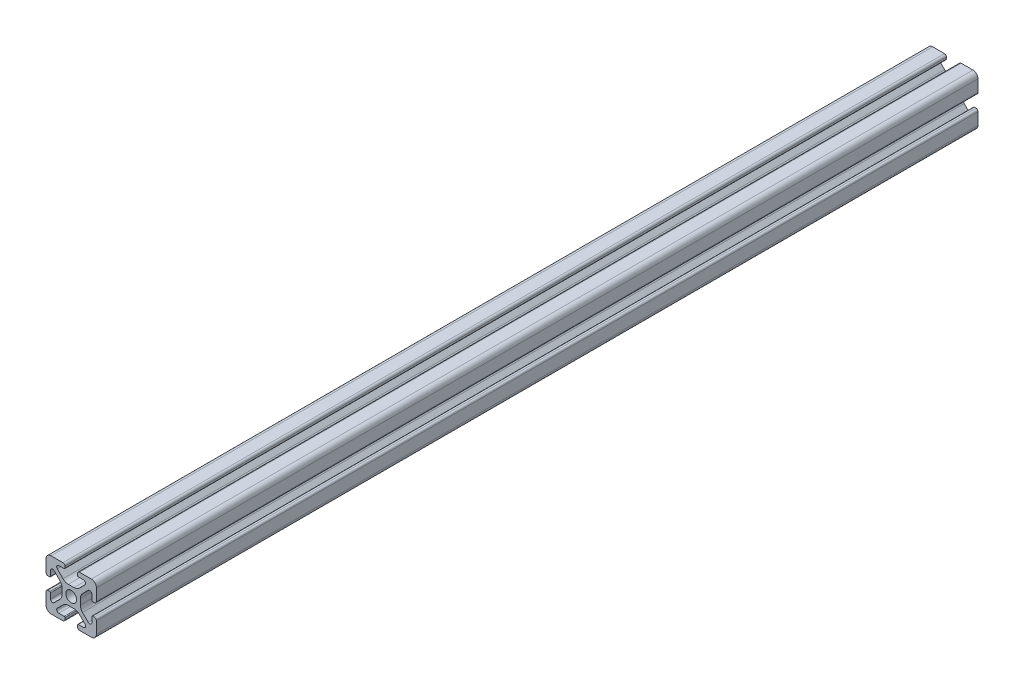
SolidWorks part; units mm, degrees
ref_plane "Front Plane" through (0, 0, 0) normal (0, 0, 1) x (1, 0, 0)
ref_plane "Top Plane" through (0, 0, 0) normal (0, 1, 0) x (1, 0, 0)
ref_plane "Right Plane" through (0, 0, 0) normal (1, 0, 0) x (0, 0, -1)
sketch "Sketch1" plane through (0, 0, 0) normal (0, 0, 1) x (1, 0, 0)
  line L2 (-9.9949, 7.9883) -> (-9.9949, 3.2893)
  line L3 (-7.9883, 9.9949) -> (-3.2893, 9.9949)
  line L4 (-2.5019, 9.2075) -> (-2.5019, 8.4963)
  line L5 (-2.8067, 8.1915) -> (-4.9149, 8.1915)
  line L6 (-5.5076, 6.7606) -> (-3.2528, 4.5058)
  line L7 (-6.7606, 5.5076) -> (-4.5058, 3.2528)
  line L8 (-8.1915, 4.9149) -> (-8.1915, 2.8067)
  line L9 (-8.4963, 2.5019) -> (-9.2075, 2.5019)
  line L11 (-1.1334, 3.6279) -> (1.1334, 3.6279)
  line L12 (-3.6279, 1.1334) -> (-3.6279, -1.1334)
  line L13 (8.4963, 2.5019) -> (9.2075, 2.5019)
  line L14 (8.1915, 4.9149) -> (8.1915, 2.8067)
  line L15 (9.9949, 7.9883) -> (9.9949, 3.2893)
  line L16 (7.9883, 9.9949) -> (3.2893, 9.9949)
  line L17 (2.5019, 9.2075) -> (2.5019, 8.4963)
  line L18 (2.8067, 8.1915) -> (4.9149, 8.1915)
  line L19 (3.6279, 1.1334) -> (3.6279, -1.1334)
  line L20 (5.5076, 6.7606) -> (3.2528, 4.5058)
  line L21 (6.7606, 5.5076) -> (4.5058, 3.2528)
  line L22 (-8.4963, -2.5019) -> (-9.2075, -2.5019)
  line L23 (-8.1915, -4.9149) -> (-8.1915, -2.8067)
  line L24 (-6.7606, -5.5076) -> (-4.5058, -3.2528)
  line L25 (-5.5076, -6.7606) -> (-3.2528, -4.5058)
  line L26 (-2.8067, -8.1915) -> (-4.9149, -8.1915)
  line L27 (-2.5019, -9.2075) -> (-2.5019, -8.4963)
  line L28 (-7.9883, -9.9949) -> (-3.2893, -9.9949)
  line L29 (-9.9949, -7.9883) -> (-9.9949, -3.2893)
  line L30 (9.9949, -7.9883) -> (9.9949, -3.2893)
  line L31 (7.9883, -9.9949) -> (3.2893, -9.9949)
  line L32 (2.5019, -9.2075) -> (2.5019, -8.4963)
  line L33 (2.8067, -8.1915) -> (4.9149, -8.1915)
  line L34 (5.5076, -6.7606) -> (3.2528, -4.5058)
  line L35 (6.7606, -5.5076) -> (4.5058, -3.2528)
  line L36 (8.1915, -4.9149) -> (8.1915, -2.8067)
  line L37 (8.4963, -2.5019) -> (9.2075, -2.5019)
  line L38 (-1.1334, -3.6279) -> (1.1334, -3.6279)
  circle A0 centre (0, 0) radius 2.1463
  arc A1 (-9.9949, 7.9883) -> (-7.9883, 9.9949) centre (-7.9883, 7.9883) cw
  arc A2 (-6.7606, 5.5076) -> (-8.1915, 4.9149) centre (-7.3533, 4.9149) ccw
  arc A3 (-4.9149, 8.1915) -> (-5.5076, 6.7606) centre (-4.9149, 7.3533) ccw
  arc A4 (-3.2893, 9.9949) -> (-2.5019, 9.2075) centre (-3.2893, 9.2075) cw
  arc A5 (-9.9949, 3.2893) -> (-9.2075, 2.5019) centre (-9.2075, 3.2893) ccw
  arc A6 (-8.1915, 2.8067) -> (-8.4963, 2.5019) centre (-8.4963, 2.8067) cw
  arc A7 (-2.5019, 8.4963) -> (-2.8067, 8.1915) centre (-2.8067, 8.4963) cw
  arc A8 (-1.1334, 3.6279) -> (-3.2528, 4.5058) centre (-1.1334, 6.6251) cw
  arc A9 (-3.6279, 1.1334) -> (-4.5058, 3.2528) centre (-6.6251, 1.1334) ccw
  arc A10 (8.1915, 2.8067) -> (8.4963, 2.5019) centre (8.4963, 2.8067) ccw
  arc A11 (9.9949, 3.2893) -> (9.2075, 2.5019) centre (9.2075, 3.2893) cw
  arc A12 (9.9949, 7.9883) -> (7.9883, 9.9949) centre (7.9883, 7.9883) ccw
  arc A13 (3.2893, 9.9949) -> (2.5019, 9.2075) centre (3.2893, 9.2075) ccw
  arc A14 (2.5019, 8.4963) -> (2.8067, 8.1915) centre (2.8067, 8.4963) ccw
  arc A15 (1.1334, 3.6279) -> (3.2528, 4.5058) centre (1.1334, 6.6251) ccw
  arc A16 (3.6279, 1.1334) -> (4.5058, 3.2528) centre (6.6251, 1.1334) cw
  arc A17 (6.7606, 5.5076) -> (8.1915, 4.9149) centre (7.3533, 4.9149) cw
  arc A18 (4.9149, 8.1915) -> (5.5076, 6.7606) centre (4.9149, 7.3533) cw
  arc A19 (-3.6279, -1.1334) -> (-4.5058, -3.2528) centre (-6.6251, -1.1334) cw
  arc A20 (-1.1334, -3.6279) -> (-3.2528, -4.5058) centre (-1.1334, -6.6251) ccw
  arc A21 (-2.5019, -8.4963) -> (-2.8067, -8.1915) centre (-2.8067, -8.4963) ccw
  arc A22 (-8.1915, -2.8067) -> (-8.4963, -2.5019) centre (-8.4963, -2.8067) ccw
  arc A23 (-9.9949, -3.2893) -> (-9.2075, -2.5019) centre (-9.2075, -3.2893) cw
  arc A24 (-3.2893, -9.9949) -> (-2.5019, -9.2075) centre (-3.2893, -9.2075) ccw
  arc A25 (-4.9149, -8.1915) -> (-5.5076, -6.7606) centre (-4.9149, -7.3533) cw
  arc A26 (-6.7606, -5.5076) -> (-8.1915, -4.9149) centre (-7.3533, -4.9149) cw
  arc A27 (-9.9949, -7.9883) -> (-7.9883, -9.9949) centre (-7.9883, -7.9883) ccw
  arc A28 (9.9949, -7.9883) -> (7.9883, -9.9949) centre (7.9883, -7.9883) cw
  arc A29 (6.7606, -5.5076) -> (8.1915, -4.9149) centre (7.3533, -4.9149) ccw
  arc A30 (4.9149, -8.1915) -> (5.5076, -6.7606) centre (4.9149, -7.3533) ccw
  arc A31 (3.2893, -9.9949) -> (2.5019, -9.2075) centre (3.2893, -9.2075) cw
  arc A32 (9.9949, -3.2893) -> (9.2075, -2.5019) centre (9.2075, -3.2893) ccw
  arc A33 (8.1915, -2.8067) -> (8.4963, -2.5019) centre (8.4963, -2.8067) cw
  arc A34 (2.5019, -8.4963) -> (2.8067, -8.1915) centre (2.8067, -8.4963) cw
  arc A35 (1.1334, -3.6279) -> (3.2528, -4.5058) centre (1.1334, -6.6251) cw
  arc A36 (3.6279, -1.1334) -> (4.5058, -3.2528) centre (6.6251, -1.1334) ccw
extrude "Boss-Extrude1" add sketch "Sketch1" along normal mid plane 350
